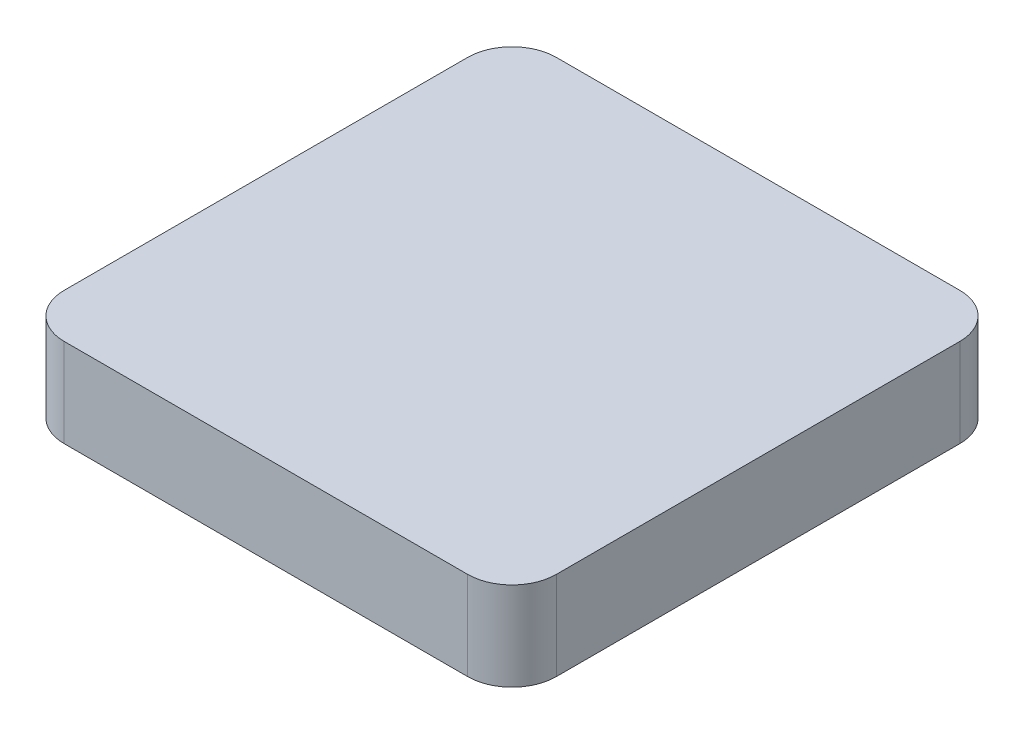
SolidWorks part; units mm, degrees
ref_plane "Front Plane" through (0, 0, 0) normal (0, 0, 1) x (1, 0, 0)
ref_plane "Top Plane" through (0, 0, 0) normal (0, 1, 0) x (1, 0, 0)
ref_plane "Right Plane" through (0, 0, 0) normal (1, 0, 0) x (0, 0, -1)
sketch "Sketch2" plane through (0, 0, 0) normal (0, 1, 0) x (1, 0, 0)
  line L0 (0, 0) -> (33.3333, 0)
  line L1 (0, 0) -> (0, 33.3333)
  line L2 (0, 33.3333) -> (33.3333, 33.3333)
  line L3 (33.3333, 0) -> (33.3333, 33.3333)
  dimension "D1" = 33.3333
extrude "Boss-Extrude1" add sketch "Sketch2" along normal blind 6
fillet "Fillet1" radius 3 4 edges at (0, 3, -33.3333) (33.3333, 3, -33.3333) (0, 3, 0) (33.3333, 3, 0)
scale "Scale1" scale about centroid uniform scaling yes scale factor 7.5
